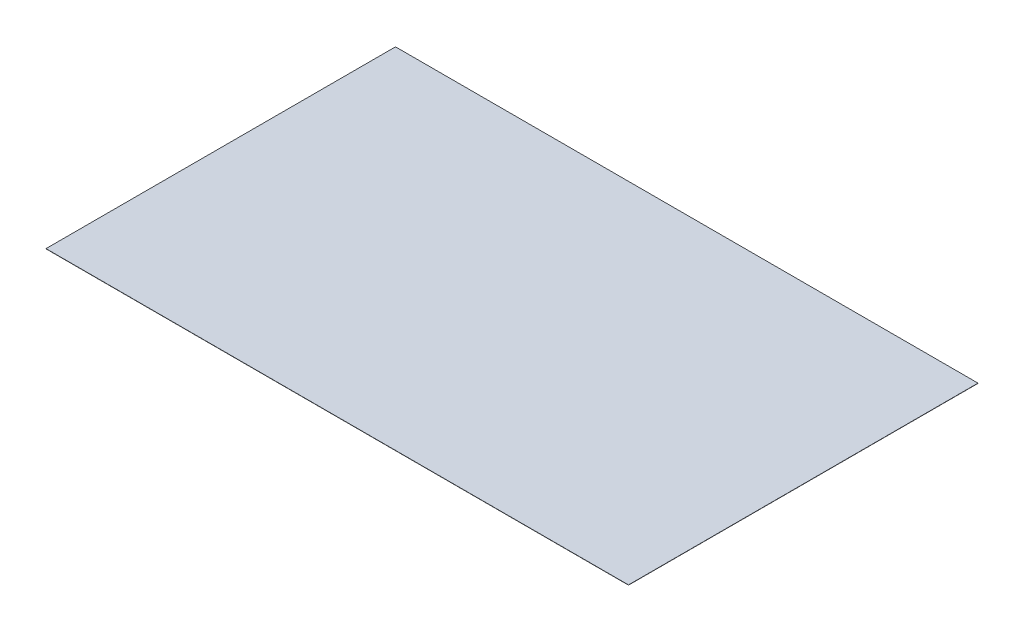
SolidWorks part; units mm, degrees
material "Epoxy Resin"
ref_plane "Front Plane" through (0, 0, 0) normal (0, 0, 1) x (1, 0, 0)
ref_plane "Top Plane" through (0, 0, 0) normal (0, 1, 0) x (1, 0, 0)
ref_plane "Right Plane" through (0, 0, 0) normal (1, 0, 0) x (0, 0, -1)
sketch "Sketch1" plane through (0, 0, 0) normal (0, 1, 0) x (1, 0, 0)
  line L1 (0, 0) -> (25, 0)
  line L2 (0, 0) -> (0, 15)
  line L3 (0, 15) -> (25, 15)
  line L4 (25, 0) -> (25, 15)
  dimension "D1" = 15
  dimension "D2" = 25
extrude "Boss-Extrude1" add sketch "Sketch1" along normal blind 0.01
sketch "Sketch2" plane through (0, 0.01, 0) normal (0, 1, 0) x (1, 0, 0)
  line L0 (6.6042, 13.4885) -> (6.8042, 13.4885)
  line L5 (4.375, 6) -> (4.8868, 6)
  line L6 (5.6042, 13.4885) -> (5.8042, 13.4885)
  line L7 (7.575, 6) -> (8.1159, 6)
  line L20 (7.6042, 13.4885) -> (7.8042, 13.4885)
  line L22 (4.375, 6) -> (4.375, 4.3194)
  line L24 (5.625, 6) -> (5.625, 4)
  line L25 (4.375, 6) -> (5.625, 4) construction
  line L26 (4.375, 4) -> (5.625, 6) construction
  line L32 (7.575, 6) -> (7.575, 4)
  line L38 (8.825, 6) -> (8.825, 4.3305)
  line L47 (10.775, 6) -> (11.3237, 6)
  line L49 (7.575, 6) -> (8.825, 4) construction
  line L50 (7.575, 4) -> (8.825, 6) construction
  line L56 (10.775, 6) -> (10.775, 4)
  line L58 (12.025, 6) -> (12.025, 5.8842)
  line L65 (10.775, 6) -> (12.025, 4) construction
  line L66 (10.775, 4) -> (12.025, 6) construction
  line L67 (4.375, 4) -> (5.625, 4)
  line L73 (6.6042, 11.7397) -> (4.8868, 11.7397)
  line L75 (10.775, 4) -> (12.025, 4)
  line L76 (7.575, 4) -> (8.825, 4)
  line L77 (8.825, 4.1273) -> (8.825, 4)
  line L78 (8.6042, 13.4885) -> (8.8042, 13.4885)
  line L79 (9.6042, 13.4885) -> (9.8042, 13.4885)
  line L80 (10.6042, 13.4885) -> (10.8042, 13.4885)
  line L88 (3.5394, 4.1189) -> (3.7394, 4.1189)
  line L89 (3.7394, 12.4048) -> (3.7394, 4.3194)
  line L90 (9.4012, 11.4059) -> (9.4012, 4.3305)
  line L91 (9.4012, 4.1273) -> (9.6012, 4.1273)
  line L96 (5.0868, 11.5422) -> (5.0868, 6)
  line L97 (0, 15) -> (0, 0) construction
  line L98 (0, 0) -> (25, 0) construction
  line L100 (8.1159, 11.213) -> (8.1159, 6)
  line L104 (11.3237, 11.8966) -> (11.3237, 6)
  line L109 (12.628, 5.8842) -> (12.025, 5.8842)
  line L113 (9.4012, 4.3305) -> (8.825, 4.3305)
  line L114 (8.825, 4.1273) -> (9.4012, 4.1273)
  line L117 (4.375, 4.3194) -> (3.7394, 4.3194)
  line L118 (3.7394, 4.1189) -> (4.375, 4.1189)
  line L124 (12.628, 12.6257) -> (12.628, 5.8842)
  line L126 (12.828, 12.6257) -> (12.828, 5.6811)
  line L127 (5.6042, 13.4885) -> (5.6042, 12.6023)
  line L129 (5.8042, 12.6023) -> (5.8042, 13.4885)
  line L130 (6.6042, 13.4885) -> (6.6042, 11.7397)
  line L132 (6.8042, 11.7397) -> (6.8042, 13.4885)
  line L135 (7.8042, 11.4105) -> (7.8042, 13.4885)
  line L138 (8.8042, 11.6034) -> (8.8042, 13.4885)
  line L141 (9.8042, 12.0941) -> (9.8042, 13.4885)
  line L142 (10.6042, 13.4885) -> (10.6042, 12.8232)
  line L144 (10.8042, 13.4885) -> (10.8042, 12.8232)
  line L145 (8.2901, 11.4105) -> (7.8042, 11.4105)
  line L146 (5.6042, 12.6023) -> (3.5394, 12.6023)
  line L147 (5.8042, 12.6023) -> (5.8042, 12.4048)
  line L148 (5.8042, 12.4048) -> (3.7394, 12.4048)
  line L150 (3.5394, 12.6023) -> (3.5394, 4.1189)
  line L152 (6.8042, 11.7397) -> (6.8042, 11.5422)
  line L153 (6.8042, 11.5422) -> (5.0868, 11.5422)
  line L156 (8.1159, 11.213) -> (7.6042, 11.213)
  line L158 (12.828, 12.8232) -> (10.8042, 12.8232)
  line L159 (12.828, 12.8232) -> (12.828, 12.6257)
  line L160 (12.628, 12.6257) -> (10.6042, 12.6257)
  line L161 (10.6042, 12.8232) -> (10.6042, 12.6257)
  line L162 (9.6012, 11.6034) -> (8.8042, 11.6034)
  line L164 (9.4012, 11.4059) -> (8.6042, 11.4059)
  line L166 (11.5104, 12.0941) -> (9.8042, 12.0941)
  line L168 (11.3237, 11.8966) -> (9.6042, 11.8966)
  line L170 (8.2901, 6) -> (8.825, 6)
  line L171 (5.0868, 6) -> (5.625, 6)
  line L172 (4.375, 4.1189) -> (4.375, 4)
  line L173 (12.025, 5.6811) -> (12.025, 4)
  line L174 (11.5104, 6) -> (12.025, 6)
  line L175 (12.025, 5.6811) -> (12.828, 5.6811)
  line L176 (9.6012, 11.6034) -> (9.6012, 4.1273)
  line L177 (4.8868, 11.7397) -> (4.8868, 6)
  line L178 (8.2901, 11.4105) -> (8.2901, 6)
  line L179 (11.5104, 12.0941) -> (11.5104, 6)
  line L180 (7.6042, 13.4885) -> (7.6042, 11.213)
  line L181 (8.6042, 13.4885) -> (8.6042, 11.4059)
  line L182 (9.6042, 13.4885) -> (9.6042, 11.8966)
  point P0 (5, 5)
  point P9 (8.2, 5)
  point P10 (11.4, 5)
  point P40 (11.4, 5)
  dimension "D1" = 0.2
  dimension "D2" = 6
  dimension "D6" = 5
  dimension "D7" = 4
  dimension "D8" = 2
  dimension "D9" = 1.25
  dimension "D10" = 3.2
  dimension "D12" = 0.2
  dimension "D11" = 3.2
extrude "Cut-Extrude1" [suppressed] cut sketch "Sketch2" against normal blind 0.01
